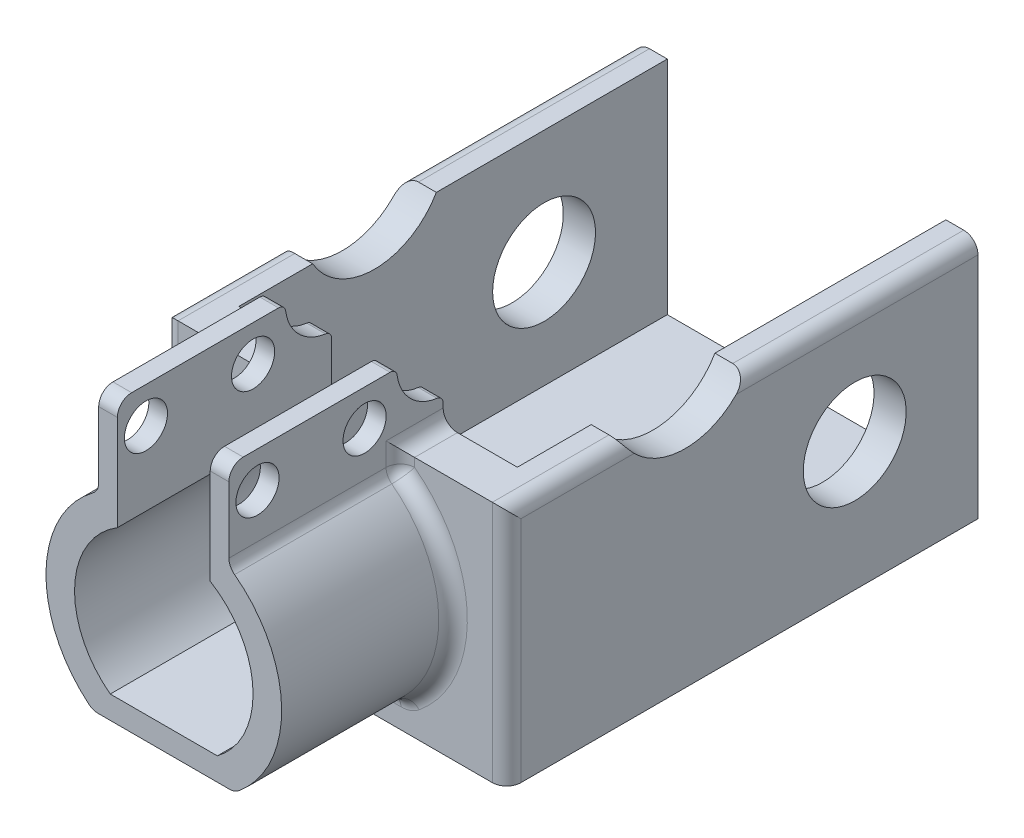
SolidWorks part; units mm, degrees
ref_plane "Front" through (0, 0, 0) normal (0, 0, 1) x (1, 0, 0)
ref_plane "Top" through (0, 0, 0) normal (0, 1, 0) x (1, 0, 0)
ref_plane "Right" through (0, 0, 0) normal (1, 0, 0) x (0, 0, -1)
sketch "Sketch1" plane through (0, 0, 0) normal (0, 0, 1) x (1, 0, 0)
  line L0 (-3.25, 71.1522) -> (-3.25, 75.4556) construction
  line L1 (4.5581, 79.1722) -> (3.25, 79.1722)
  line L2 (3.25, 79.1722) -> (3.25, 71.4895)
  line L3 (3.3148, 71.1522) -> (-3.3148, 71.1522) construction
  line L4 (-4.5581, 73.0275) -> (-4.5581, 79.1722)
  line L5 (-4.5581, 79.1722) -> (-3.25, 79.1722)
  line L8 (-5, 61.1522) -> (5, 61.1522) construction
  line L9 (3.7483, 61.1522) -> (-3.7483, 61.1522)
  line L10 (-3.25, 79.1722) -> (-3.25, 71.4895)
  line L11 (4.948, 59.5519) -> (-4.948, 59.5519)
  line L12 (0.75, 79.1722) -> (-0.1, 79.1722) construction
  line L16 (0, 71.1522) -> (0, 51.7777) construction
  line L17 (4.5581, 73.0275) -> (4.5581, 79.1722)
  line L20 (-5, 71.1522) -> (5, 71.1522) construction
  arc A1 (-3.5984, 61.3522) -> (-3.0574, 60.9907) centre (0, 66.1522) ccw construction
  arc A4 (-3.3148, 71.1522) -> (-3.5984, 61.3522) centre (0, 66.1522) ccw construction
  arc A5 (-3.5984, 61.3522) -> (-3.3163, 61.1532) centre (0, 66.1522) ccw construction
  arc A7 (3.3148, 61.1522) -> (3.3148, 71.1522) centre (0, 66.1522) ccw construction
  arc A8 (3.25, 71.4895) -> (3.7483, 61.1522) centre (0, 66.1522) cw
  arc A9 (4.5581, 73.0275) -> (4.948, 59.5519) centre (0, 66.1522) cw
  arc A10 (-4.5581, 73.0275) -> (-4.948, 59.5519) centre (0, 66.1522) ccw
  arc A14 (-3.25, 71.4895) -> (-3.7483, 61.1522) centre (0, 66.1522) ccw
  arc A16 (-3.453, 71.3605) -> (-3.7483, 61.1522) centre (0, 66.1522) ccw construction
  arc A17 (5.8778, 67.3521) -> (3.3162, 71.1512) centre (0, 66.1522) ccw construction
  arc A18 (-5.8778, 64.9523) -> (-3.3162, 61.1531) centre (0, 66.1522) ccw construction
  arc A19 (-3.7483, 61.1522) -> (-3.1848, 60.7756) centre (0, 66.1522) ccw construction
  arc A20 (-4.948, 59.5519) -> (-4.2041, 59.0548) centre (0, 66.1522) ccw construction
  dimension "D1" = 2.25
  dimension "D2" = 0.25
extrude "Boss-Extrude1" add sketch "Sketch1" along normal up to surface (6.1008 mm away) and the other way up to surface (8.8992 mm away)
sketch "Sketch2" plane through (-4.5581, 0, 0) normal (-1, 0, 0) x (0, 0, 1)
  circle A1 centre (4.1008, 76.6622) radius 1.51
  circle A3 centre (-3.3992, 76.6622) radius 1.51
  circle A4 centre (-3.3992, 76.6622) radius 1.51 construction
  circle A5 centre (4.1008, 76.6622) radius 1.51 construction
extrude "Cut-Extrude1" cut sketch "Sketch2" against normal through all
fillet "Fillet1" radius 1 8 edges at (-4.948, 59.5519, -1.3992) (4.948, 59.5519, -1.3992) (4.5581, 73.0275, -1.3992) (3.904, 79.1722, 6.1008) (3.904, 79.1722, -8.8992) (-3.904, 79.1722, -8.8992) (-3.904, 79.1722, 6.1008) (-4.5581, 73.0275, -1.3992)
sketch "Sketch3" plane through (0, 0, -8.8992) normal (0, 0, -1) x (-1, 0, 0)
  line L0 (0, 71.1522) -> (0, 61.1522) construction
  line L1 (-6, 66.1522) -> (6, 66.1522) construction
  line L2 (6, 70.1522) -> (6, 62.1522) construction
  line L3 (-12, 74.1522) -> (12, 74.1522)
  line L4 (5, 71.1522) -> (-5, 71.1522)
  line L5 (-6, 70.1522) -> (-6, 62.1522)
  line L6 (-5, 61.1522) -> (5, 61.1522)
  line L7 (6, 62.1522) -> (6, 70.1522)
  line L8 (5, 71.1522) -> (-5, 71.1522) construction
  line L9 (-6, 70.1522) -> (-6, 62.1522) construction
  line L10 (-5, 61.1522) -> (5, 61.1522) construction
  line L11 (6, 62.1522) -> (6, 70.1522) construction
  line L12 (-12, 74.1522) -> (-12, 57.1522)
  line L13 (-12, 57.1522) -> (12, 57.1522)
  line L14 (12, 74.1522) -> (12, 57.1522)
  arc A0 (0.1395, 73.858) -> (-0.1395, 73.858) centre (0, 66.1522) ccw construction
  arc A1 (0.1395, 73.858) -> (-0.1395, 73.858) centre (0, 66.1522) ccw construction
  arc A4 (6, 70.1522) -> (5, 71.1522) centre (5, 70.1522) ccw
  arc A5 (-5, 71.1522) -> (-6, 70.1522) centre (-5, 70.1522) ccw
  arc A6 (-6, 62.1522) -> (-5, 61.1522) centre (-5, 62.1522) ccw
  arc A7 (5, 61.1522) -> (6, 62.1522) centre (5, 62.1522) ccw
  arc A8 (6, 70.1522) -> (5, 71.1522) centre (5, 70.1522) ccw construction
  arc A9 (-5, 71.1522) -> (-6, 70.1522) centre (-5, 70.1522) ccw construction
  arc A10 (-6, 62.1522) -> (-5, 61.1522) centre (-5, 62.1522) ccw construction
  arc A11 (5, 61.1522) -> (6, 62.1522) centre (5, 62.1522) ccw construction
  point P20 (0, 74.1522)
  dimension "D2" = 3
  dimension "D3" = 6
  dimension "D4" = 4
  dimension "D1" = 0
extrude "Boss-Extrude2" add sketch "Sketch3" along normal blind 30 and the other way blind 3
sketch "Sketch4" plane through (0, 0, -38.8992) normal (0, 0, -1) x (-1, 0, 0)
  line L0 (12, 74.1522) -> (-12, 74.1522) construction
  line L1 (-9.75, 74.1522) -> (9.75, 74.1522)
  line L2 (-9.75, 74.1522) -> (-9.75, 58.6522)
  line L3 (-9.75, 58.6522) -> (9.75, 58.6522)
  line L4 (9.75, 74.1522) -> (9.75, 58.6522)
  line L5 (-12, 57.1522) -> (12, 57.1522) construction
  line L6 (-12, 74.1522) -> (-12, 57.1522) construction
  point P6 (0, 74.1522)
  point P9 (0, 57.1522)
  dimension "D1" = 2.25
  dimension "D2" = 1.5
extrude "Cut-Extrude2" cut sketch "Sketch4" against normal up to surface (30 mm away) up to face at (3.904, 76.1622, -8.8992)
sketch "Sketch6" plane through (0, 0, -8.8992) normal (0, 0, -1) x (-1, 0, 0)
  line L0 (-3.25, 74.1522) -> (3.25, 74.1522) construction
  line L5 (-3.25, 74.1522) -> (-3.25, 71.4895)
  line L7 (-12, 57.1522) -> (12, 57.1522) construction
  line L12 (3.25, 74.1522) -> (-3.25, 74.1522)
  line L13 (0, 57.1522) -> (0, 79.2715) construction
  line L14 (3.25, 74.1522) -> (3.25, 71.4895)
  line L16 (3.7483, 61.1522) -> (-3.7483, 61.1522) construction
  line L17 (3.7483, 61.1522) -> (-3.7483, 61.1522)
  arc A12 (-3.25, 71.4895) -> (-3.7483, 61.1522) centre (0, 66.1522) ccw construction
  arc A13 (3.7483, 61.1522) -> (3.25, 71.4895) centre (0, 66.1522) ccw construction
  arc A14 (-3.25, 71.4895) -> (-3.7483, 61.1522) centre (0, 66.1522) ccw
  arc A15 (3.7483, 61.1522) -> (3.25, 71.4895) centre (0, 66.1522) ccw
extrude "Cut-Extrude6" cut sketch "Sketch6" against normal up to surface (3 mm away) up to face at (0, 67.292, -5.8992)
fillet "Fillet2" radius 1 15 edges at (4.5581, 73.8485, -5.8992) (4.6634, 73.0981, -5.8992) (-4.5581, 73.8485, -5.8992) (-4.6634, 73.0981, -5.8992) (-8.2471, 66.3306, -5.8992) (-4.94, 59.6105, -5.8992) (0, 59.5519, -5.8992) (4.94, 59.6105, -5.8992) (8.2471, 66.3306, -5.8992) (-12, 74.1522, -22.3992) (12, 74.1522, -22.3992) (12, 65.6522, -5.8992) (-12, 65.6522, -5.8992) (-4.5581, 74.1522, -7.3992) (4.5581, 74.1522, -7.3992)
sketch "Sketch7" plane through (-12, 0, 0) normal (-1, 0, 0) x (0, 0, 1)
  arc A0 (-29.7976, 67.6808) -> (-28.7698, 65.5966) centre (-30.2703, 66.1522) ccw construction
  circle A1 centre (-30.2703, 66.1522) radius 1.6 construction
  circle A2 centre (-30.2703, 66.1522) radius 3.6
  dimension "D1" = 7.2
extrude "Cut-Extrude7" cut sketch "Sketch7" against normal through all
sketch "Sketch8" plane through (12, 0, 0) normal (1, 0, 0) x (0, 0, -1)
  line L1 (5.8992, 74.1522) -> (38.8992, 74.1522) construction
  line L2 (5.8992, 57.1522) -> (5.8992, 74.1522) construction
  line L4 (14.0691, 74.1522) -> (22.7293, 74.1522)
  arc A0 (14.0691, 74.1522) -> (22.7293, 74.1522) centre (18.3992, 76.6522) ccw
  dimension "D1" = 5
  dimension "D2" = 12.5
  dimension "D3" = 2.5
extrude "Cut-Extrude8" cut sketch "Sketch8" against normal through all and the other way through all
sketch "Sketch9" plane through (-4.5581, 0, 0) normal (-1, 0, 0) x (0, 0, 1)
  line L0 (5.1008, 79.1722) -> (-7.8992, 79.1722) construction
  line L1 (-8.8992, 78.1722) -> (-8.8992, 75.1522) construction
  line L2 (-5.6492, 81.9268) -> (-5.6492, 76.2687) construction
  line L3 (-10.7252, 75.9222) -> (-6.0426, 75.9222) construction
  line L4 (-8.8992, 78.1722) -> (-8.8992, 75.9222)
  line L5 (-5.6492, 79.1722) -> (-7.8992, 79.1722)
  arc A0 (-5.6492, 79.1722) -> (-8.8992, 75.9222) centre (-8.8992, 79.1722) cw
  arc A1 (-7.8992, 79.1722) -> (-8.8992, 78.1722) centre (-7.8992, 78.1722) ccw construction
  arc A2 (-7.8992, 79.1722) -> (-8.8992, 78.1722) centre (-7.8992, 78.1722) ccw
  dimension "D1" = 3.25
extrude "Cut-Extrude9" cut sketch "Sketch9" against normal through all
fillet "Fillet3" radius 0.5 4 edges at (-3.904, 75.9222, -8.8992) (3.904, 75.9222, -8.8992) (3.904, 79.1722, -5.6492) (-3.904, 79.1722, -5.6492)
ref_plane "Plane1" through (0, 0, 0) normal (-1, 0, 0) x (0, 0, 1)
sketch "Sketch10" plane through (-12, 0, 0) normal (-1, 0, 0) x (0, 0, 1)
  line L0 (6.1008, 59.7793) -> (6.1008, 72.7455) construction
  line L1 (6.1008, 59.7793) -> (6.1008, 72.7455)
  line L2 (-30.2703, 66.1522) -> (6.1008, 66.2624) construction
  line L3 (6.1008, 73.5448) -> (6.1008, 78.1722) construction
  line L4 (5.1008, 79.1722) -> (-5.1827, 79.1722) construction
  circle A0 centre (-30.2703, 66.1522) radius 3.6 construction
  circle A1 centre (-30.2703, 66.1522) radius 3.6
  arc A2 (-14.8285, 73.1522) -> (-14.0691, 74.1522) centre (-18.3992, 76.6522) ccw construction
  arc A3 (-22.7293, 74.1522) -> (-21.9699, 73.1522) centre (-18.3992, 76.6522) ccw construction
  arc A4 (-21.9699, 73.1522) -> (-14.8285, 73.1522) centre (-18.3992, 76.6522) ccw construction
  arc A5 (-14.8285, 73.1522) -> (-14.0691, 74.1522) centre (-18.3992, 76.6522) ccw
  arc A6 (-22.7293, 74.1522) -> (-21.9699, 73.1522) centre (-18.3992, 76.6522) ccw
  arc A7 (-21.9699, 73.1522) -> (-14.8285, 73.1522) centre (-18.3992, 76.6522) ccw
  circle A8 centre (4.1008, 76.6622) radius 1.51 construction
  circle A9 centre (-3.3992, 76.6622) radius 1.51 construction
  circle A10 centre (4.1008, 76.6622) radius 1.51
  circle A11 centre (-3.3992, 76.6622) radius 1.51
  point P19 (0, 0)
  point P20 (0, 0)
  point P23 (0, 0)
  dimension "D3" = 5
  dimension "D4" = 7.2
  dimension "D5" = 3.02
  dimension "D1" = 36.371
  dimension "D2" = 24.5
  dimension "D6" = 7.5
  dimension "D7" = 2
  dimension "D8" = 2.51
